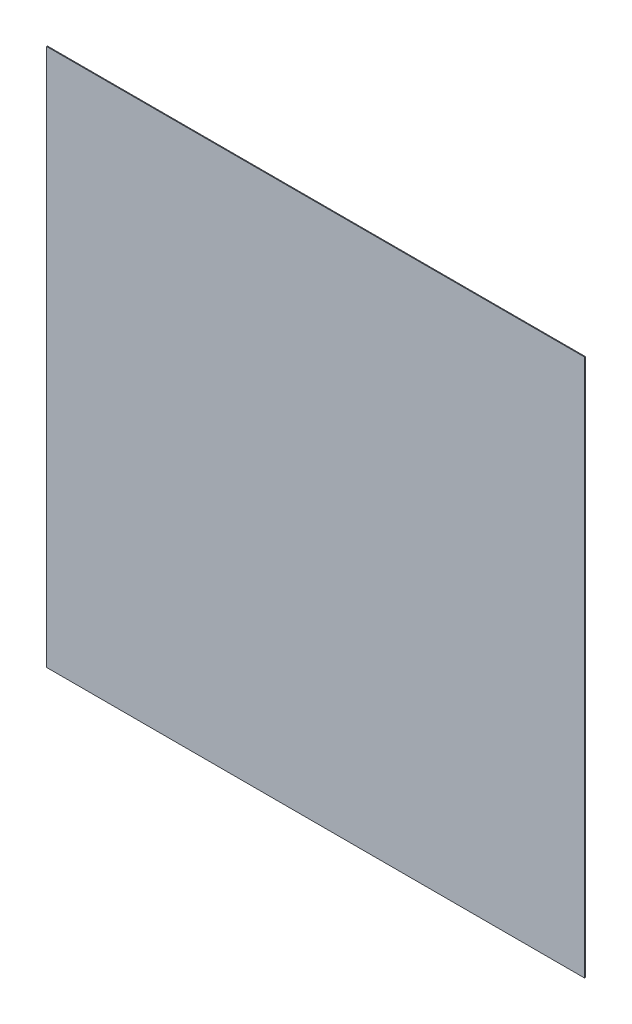
SolidWorks part; units mm, degrees
material "Polyethylene Cross-Linked"
ref_plane "Front Plane" through (0, 0, 0) normal (0, 0, 1) x (1, 0, 0)
ref_plane "Top Plane" through (0, 0, 0) normal (0, 1, 0) x (1, 0, 0)
ref_plane "Right Plane" through (0, 0, 0) normal (1, 0, 0) x (0, 0, -1)
sketch "Sketch1" plane through (0, 0, 0) normal (0, 0, 1) x (1, 0, 0)
  line L1 (-31.75, 31.75) -> (31.75, 31.75)
  line L2 (-31.75, 31.75) -> (-31.75, -31.75)
  line L3 (-31.75, -31.75) -> (31.75, -31.75)
  line L4 (31.75, 31.75) -> (31.75, -31.75)
  dimension "D1" = 63.5
  dimension "D2" = 63.5
  dimension "D3" = 31.75
  dimension "D4" = 31.75
extrude "Boss-Extrude1" add sketch "Sketch1" along normal blind 0.1
